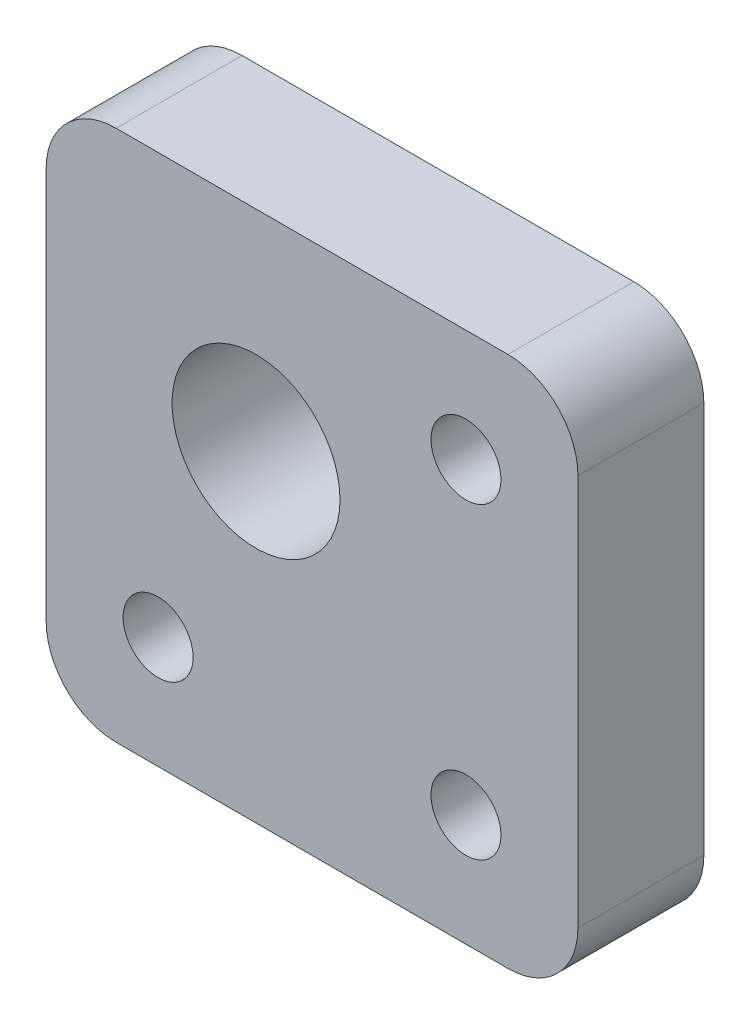
SolidWorks part; units mm, degrees
ref_plane "前视基准面" through (0, 0, 0) normal (0, 0, 1) x (1, 0, 0)
ref_plane "上视基准面" through (0, 0, 0) normal (0, 1, 0) x (1, 0, 0)
ref_plane "右视基准面" through (0, 0, 0) normal (1, 0, 0) x (0, 0, -1)
sketch "草图1" plane through (0, 0, 0) normal (0, 0, 1) x (1, 0, 0)
  line L0 (-2.1698, 45.9569) -> (-2.1698, -29.846) construction
  line L1 (-21.1698, 19.8398) -> (16.8302, 19.8398)
  line L2 (-21.1698, 19.8398) -> (-21.1698, -18.1602)
  line L3 (-21.1698, -18.1602) -> (16.8302, -18.1602)
  line L4 (16.8302, 19.8398) -> (16.8302, -18.1602)
  line L9 (-60.3251, 0.8398) -> (50.8197, 0.8398) construction
  line L11 (-13.1698, 11.8398) -> (8.8302, 11.8398) construction
  line L12 (-13.1698, 11.8398) -> (-13.1698, -10.1602) construction
  line L13 (-13.1698, -10.1602) -> (8.8302, -10.1602) construction
  line L14 (8.8302, 11.8398) -> (8.8302, -10.1602) construction
  circle A0 centre (8.8302, 11.8398) radius 2.5
  circle A1 centre (8.8302, -10.1602) radius 2.5
  circle A2 centre (-13.1698, -10.1602) radius 2.5
  circle A3 centre (-6.1698, 4.8398) radius 6
  dimension "D4" = 5
  dimension "D5" = 15
  dimension "D6" = 15
  dimension "D7" = 12
  dimension "D1" = 38
  dimension "D2" = 8
  dimension "D3" = 8
extrude "凸台-拉伸1" add sketch "草图1" along normal blind 9
fillet "圆角1" radius 5 4 edges at (-21.1698, 19.8398, 4.5) (-21.1698, -18.1602, 4.5) (16.8302, -18.1602, 4.5) (16.8302, 19.8398, 4.5)
